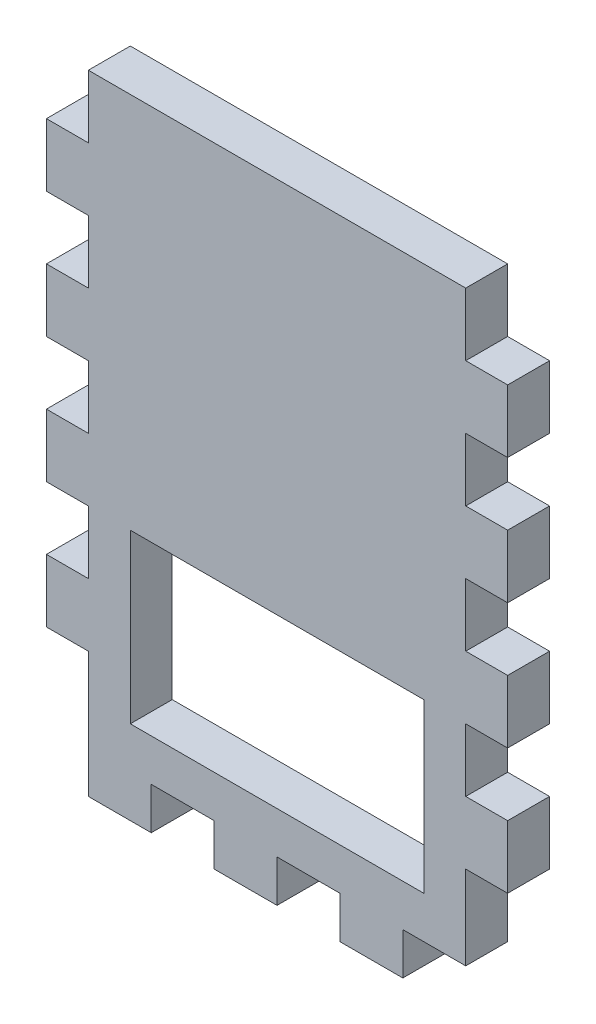
SolidWorks part; units mm, degrees
material "Pine"
ref_plane "Front Plane" through (0, 0, 0) normal (0, 0, 1) x (1, 0, 0)
ref_plane "Top Plane" through (0, 0, 0) normal (0, 1, 0) x (1, 0, 0)
ref_plane "Right Plane" through (0, 0, 0) normal (1, 0, 0) x (0, 0, -1)
sketch "Sketch1" plane through (0, 0, 0) normal (0, 0, 1) x (1, 0, 0)
  line L1 (0, 0) -> (57.15, 0)
  line L2 (0, 0) -> (0, -88.9)
  line L3 (0, -88.9) -> (57.15, -88.9)
  line L4 (57.15, 0) -> (57.15, -88.9)
  line L5 (6.35, -57.15) -> (50.8, -57.15)
  line L6 (6.35, -57.15) -> (6.35, -82.55)
  line L7 (6.35, -82.55) -> (50.8, -82.55)
  line L8 (50.8, -57.15) -> (50.8, -82.55)
  dimension "D1" = 88.9
  dimension "D2" = 57.15
  dimension "D4" = 25.4
  dimension "D5" = 44.45
  dimension "D8" = 6.35
  dimension "D9" = 6.35
extrude "Boss-Extrude1" add sketch "Sketch1" along normal blind 6.35
sketch "Sketch2" plane through (0, 0, 6.35) normal (0, 0, 1) x (1, 0, 0)
  line L0 (0, 0) -> (0, -88.9) construction
  line L1 (0, -9.525) -> (-6.35, -9.525)
  line L2 (0, -9.525) -> (0, -19.05)
  line L3 (0, -19.05) -> (-6.35, -19.05)
  line L4 (-6.35, -9.525) -> (-6.35, -19.05)
  line L5 (57.15, 0) -> (0, 0) construction
  line L6 (0, -28.575) -> (0, -38.1)
  line L7 (0, -28.575) -> (-6.35, -28.575)
  line L8 (-6.35, -28.575) -> (-6.35, -38.1)
  line L9 (0, -38.1) -> (-6.35, -38.1)
  line L10 (0, -47.625) -> (0, -57.15)
  line L11 (0, -47.625) -> (-6.35, -47.625)
  line L12 (-6.35, -47.625) -> (-6.35, -57.15)
  line L13 (0, -57.15) -> (-6.35, -57.15)
  line L14 (0, -66.675) -> (0, -76.2)
  line L15 (0, -66.675) -> (-6.35, -66.675)
  line L16 (-6.35, -66.675) -> (-6.35, -76.2)
  line L17 (0, -76.2) -> (-6.35, -76.2)
  line L23 (0, -88.9) -> (9.525, -88.9)
  line L24 (0, -88.9) -> (0, -95.25)
  line L25 (0, -95.25) -> (9.525, -95.25)
  line L26 (9.525, -88.9) -> (9.525, -95.25)
  line L27 (19.05, -88.9) -> (19.05, -95.25)
  line L28 (19.05, -88.9) -> (28.575, -88.9)
  line L29 (28.575, -88.9) -> (28.575, -95.25)
  line L30 (19.05, -95.25) -> (28.575, -95.25)
  line L31 (38.1, -88.9) -> (38.1, -95.25)
  line L32 (38.1, -88.9) -> (47.625, -88.9)
  line L33 (47.625, -88.9) -> (47.625, -95.25)
  line L34 (38.1, -95.25) -> (47.625, -95.25)
  line L39 (28.575, 0) -> (28.575, -88.9) construction
  line L56 (57.15, -19.05) -> (63.5, -19.05)
  line L57 (57.15, -88.9) -> (57.15, -95.25) [skipped]
  line L58 (57.15, -95.25) -> (66.675, -95.25) [skipped]
  line L59 (66.675, -88.9) -> (66.675, -95.25) [skipped]
  line L60 (57.15, -88.9) -> (66.675, -88.9) [skipped]
  line L61 (63.5, -9.525) -> (63.5, -19.05)
  line L62 (57.15, -9.525) -> (63.5, -9.525)
  line L63 (57.15, -9.525) -> (57.15, -19.05)
  line L64 (57.15, -28.575) -> (63.5, -28.575)
  line L65 (63.5, -28.575) -> (63.5, -38.1)
  line L66 (57.15, -38.1) -> (63.5, -38.1)
  line L67 (57.15, -28.575) -> (57.15, -38.1)
  line L68 (57.15, -66.675) -> (63.5, -66.675)
  line L69 (63.5, -66.675) -> (63.5, -76.2)
  line L70 (57.15, -76.2) -> (63.5, -76.2)
  line L71 (57.15, -66.675) -> (57.15, -76.2)
  line L72 (57.15, -47.625) -> (63.5, -47.625)
  line L73 (63.5, -47.625) -> (63.5, -57.15)
  line L74 (57.15, -57.15) -> (63.5, -57.15)
  line L75 (57.15, -47.625) -> (57.15, -57.15)
  dimension "D1" = 6.35
  dimension "D2" = 9.525
  dimension "D3" = 9.525
  dimension "D5" = 9.525
  dimension "D6" = 6.35
  dimension "D8" = 9.525
  dimension "D9" = 4
  dimension "D10" = 9.525
  dimension "D4" = 4
extrude "Boss-Extrude3" add sketch "Sketch2" against normal up to surface (6.35 mm away) up to face at (28.575, -44.45, 0)
